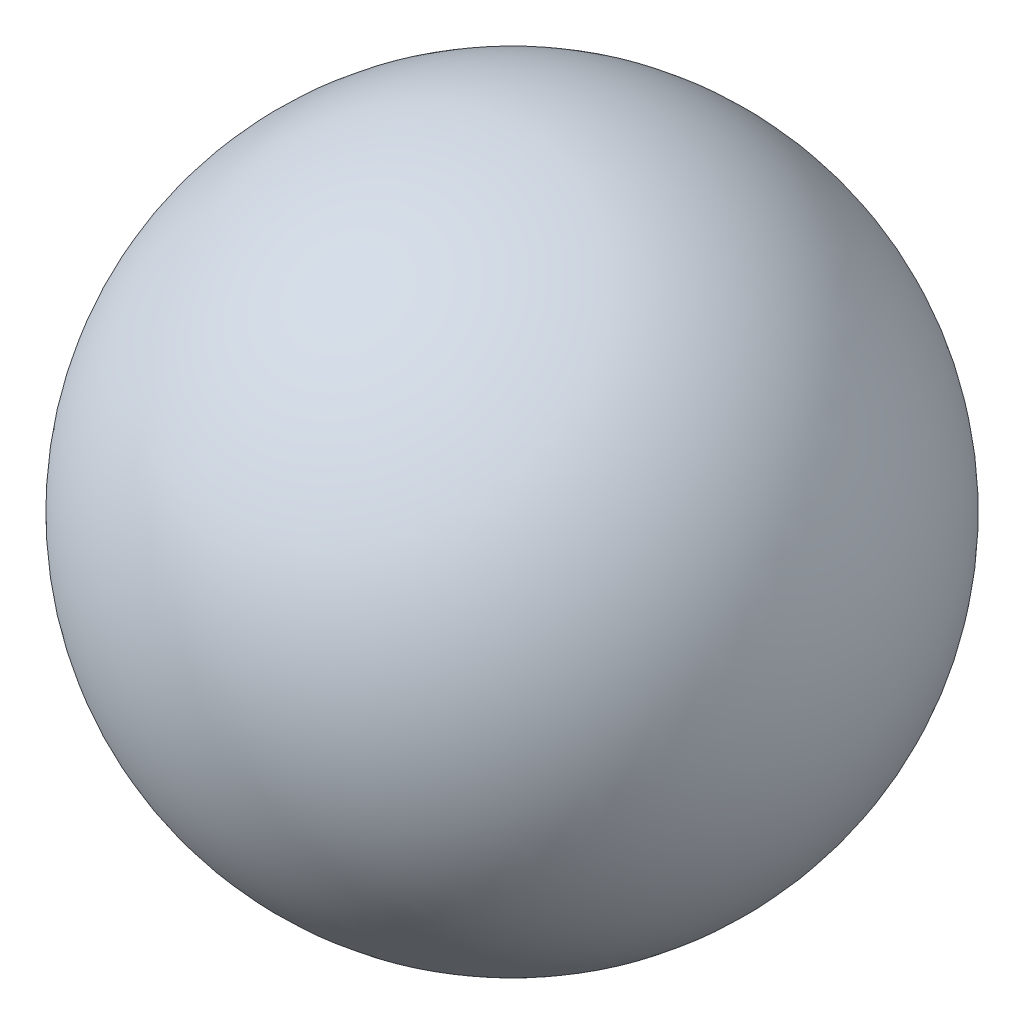
SolidWorks part; units mm, degrees
material "3.0205 (EN-AW 1200)"
ref_plane "Piano frontale" through (0, 0, 0) normal (0, 0, 1) x (1, 0, 0)
ref_plane "Piano superiore" through (0, 0, 0) normal (0, 1, 0) x (1, 0, 0)
ref_plane "Piano destro" through (0, 0, 0) normal (1, 0, 0) x (0, 0, -1)
sketch "Schizzo1" plane through (0, 0, 0) normal (1, 0, 0) x (0, 0, -1)
  line L0 (0, -26) -> (0, 26)
  arc A0 (0, 26) -> (0, -26) centre (0, 0) cw
  dimension "D1" = 26
revolve "Rivoluzione1" add sketch "Schizzo1" angle 360 about L0
